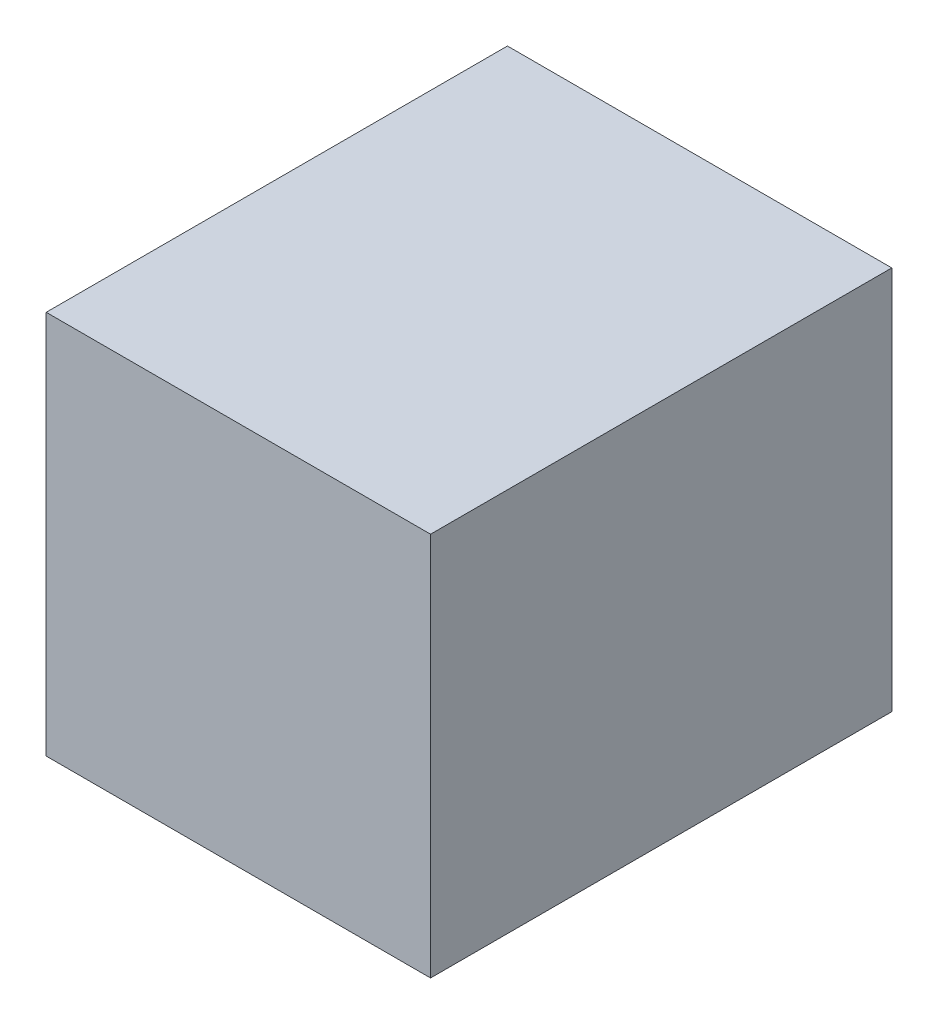
SolidWorks part; units mm, degrees
material "Plain Carbon Steel"
ref_plane "Front Plane" through (0, 0, 0) normal (0, 0, 1) x (1, 0, 0)
ref_plane "Top Plane" through (0, 0, 0) normal (0, 1, 0) x (1, 0, 0)
ref_plane "Right Plane" through (0, 0, 0) normal (1, 0, 0) x (0, 0, -1)
sketch "Sketch1" plane through (0, 0, 0) normal (0, 0, 1) x (1, 0, 0)
  line L1 (0, 0) -> (9.525, 0)
  line L2 (0, 0) -> (0, 9.525)
  line L3 (0, 9.525) -> (9.525, 9.525)
  line L4 (9.525, 0) -> (9.525, 9.525)
  dimension "D1" = 9.525
  dimension "D2" = 9.525
extrude "Boss-Extrude1" add sketch "Sketch1" along normal up to surface (11.43 mm away)
